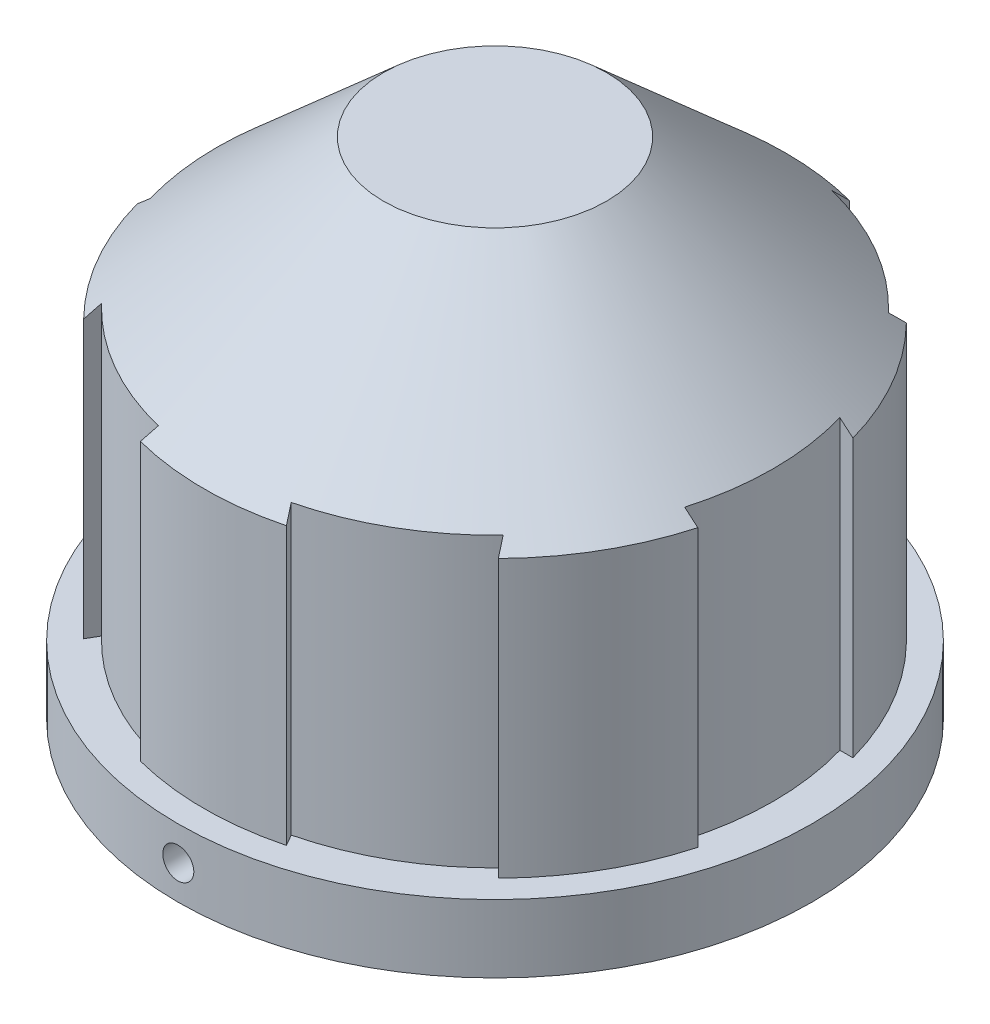
SolidWorks part; units mm, degrees
ref_plane "Front Plane" through (0, 0, 0) normal (0, 0, 1) x (1, 0, 0)
ref_plane "Top Plane" through (0, 0, 0) normal (0, 1, 0) x (1, 0, 0)
ref_plane "Right Plane" through (0, 0, 0) normal (1, 0, 0) x (0, 0, -1)
sketch "Sketch1" plane through (0, 0, 0) normal (0, 0, 1) x (1, 0, 0)
  line L0 (16.35, 0) -> (16.35, 3.5)
  line L1 (16.35, 3.5) -> (15, 3.5)
  line L2 (15, 3.5) -> (15, 17.7785)
  line L3 (15, 17.7785) -> (5.75, 26)
  line L4 (5.75, 26) -> (-0.0162, 26)
  line L5 (0, 0) -> (0, 31.4223) construction
  line L6 (16.35, 0) -> (12.75, 0)
  line L7 (12.75, 0) -> (12.75, 17.1025)
  line L8 (12.75, 17.1025) -> (5.6965, 23.3717)
  line L9 (5.6965, 23.3717) -> (4.5, 5)
  line L10 (4.5, 5) -> (3.425, 5)
  line L11 (3.425, 5) -> (3.0846, 24.5)
  line L12 (3.0846, 24.5) -> (0, 24.5)
  line L13 (0, 24.5) -> (-0.0162, 26)
  dimension "D1" = 32.7
  dimension "D2" = 3.5
  dimension "D3" = 25.5
  dimension "D4" = 6.85
  dimension "D5" = 9
  dimension "D6" = 11.5
  dimension "D7" = 30
  dimension "D8" = 91
  dimension "D9" = 2
  dimension "D10" = 24.5
  dimension "D11" = 26
  dimension "D12" = 5
revolve "Revolve3" add sketch "Sketch1" angle 360 about L5
sketch "Sketch2" plane through (0, 26, 0) normal (0, 1, 0) x (1, 0, 0)
  line L0 (14.35, 0) -> (15, 0) construction
  line L1 (13.7812, -4) -> (14.4568, -4)
  line L2 (13.7812, 4) -> (14.4568, 4)
  line L3 (0, 4) -> (20.7165, 4) construction
  line L4 (0, 0) -> (20.7165, 0) construction
  line L5 (0, -4) -> (20.7165, -4) construction
  arc A0 (14.4568, -4) -> (14.4568, 4) centre (0, 0) ccw
  arc A1 (13.7812, -4) -> (13.7812, 4) centre (0, 0) ccw
  dimension "D1" = 28.7
  dimension "D2" = 4
  dimension "D3" = 4
extrude "Cut-Extrude1" cut sketch "Sketch2" against normal up to surface (22.5 mm away) up to face at (0, 3.5, -15)
pattern_circular "CirPattern1" count 6 over 360 about axis through (0, 0, 0) along (0, 1, 0) of "Cut-Extrude1"
ref_plane "Plane1" through (0, 0, 16.35) normal (0, 0, 1) x (1, 0, 0)
hole_wizard "M2x0.4 Tapped Hole1" positions "Sketch3" profile "Sketch4" tap size "M2x0.4" standard "ANSI Metric"
sketch "Sketch3" plane through (0, 0, 16.35) normal (0, 0, 1) x (1, 0, 0)
  point P0 (0, 1.75)
  dimension "D1" = 1.75
sketch "Sketch4" plane through (0, 1.75, 16.35) normal (1, 0, 0) x (0, -1, 0)
  line L0 (0, 0) -> (0, 7.4807)
  line L1 (0, 7.4807) -> (0.8, 7)
  line L2 (0.8, 7) -> (0.8, 0)
  line L5 (0.8, 0) -> (0, 0)
  line L10 (0, 7.4807) -> (-0.8, 7) construction
  line L11 (0, -6.35) -> (0, 107.95) construction
  dimension "Tap Drill Dia." = 1.6
  dimension "Tap Drill Depth" = 7
  dimension "Drill Angle" = 118
cosmetic thread "Hole Thread1" parameters "D1"=3.6251, "D2"=2
ref_plane "Plane2" through (0, 0, -16.35) normal (0, 0, -1) x (-1, 0, 0)
hole_wizard "M2x0.4 Tapped Hole2" positions "Sketch5" profile "Sketch6" tap size "M2x0.4" standard "ANSI Metric"
sketch "Sketch5" plane through (0, 0, -16.35) normal (0, 0, -1) x (-1, 0, 0)
  point P0 (0, 1.75)
  dimension "D1" = 1.75
sketch "Sketch6" plane through (0, 1.75, -16.35) normal (1, 0, 0) x (0, 1, 0)
  line L0 (0, 0) -> (0, 8.6807)
  line L1 (0, 8.6807) -> (0.8, 8.2)
  line L2 (0.8, 8.2) -> (0.8, 0)
  line L5 (0.8, 0) -> (0, 0)
  line L10 (0, 8.6807) -> (-0.8, 8.2) construction
  line L11 (0, -6.35) -> (0, 107.95) construction
  dimension "Tap Drill Dia." = 1.6
  dimension "Tap Drill Depth" = 8.2
  dimension "Drill Angle" = 118
cosmetic thread "Hole Thread2" parameters "D1"=3.6251, "D2"=2
